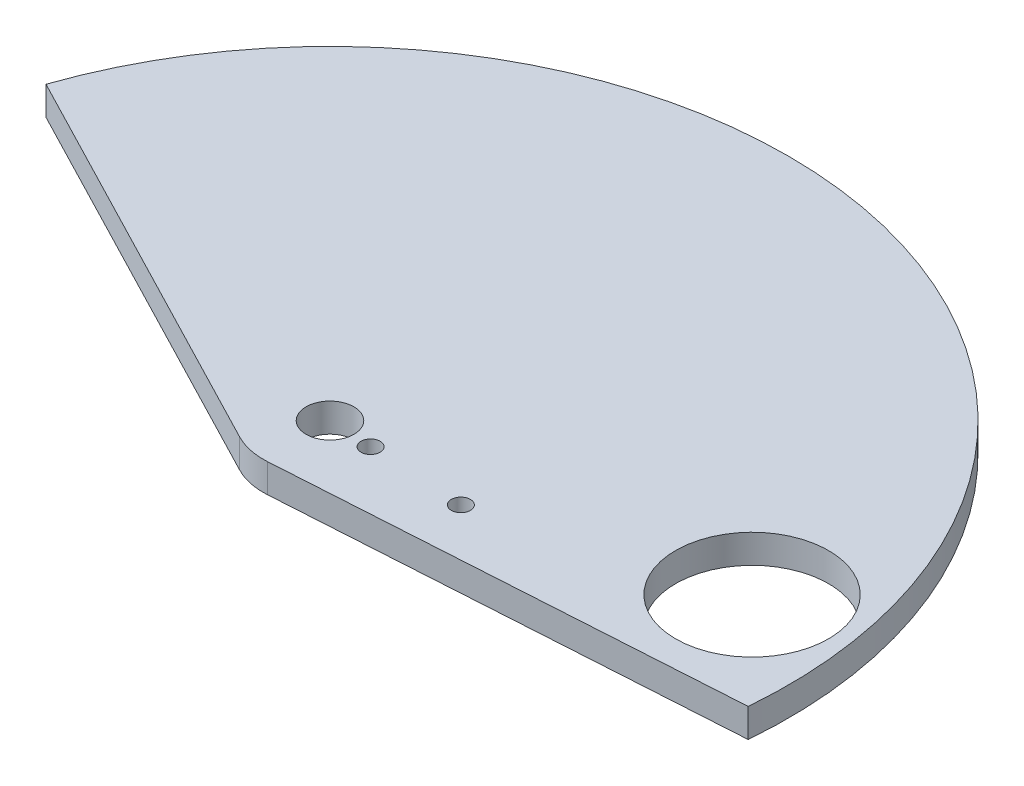
SolidWorks part; units mm, degrees
ref_plane "Front Plane" through (0, 0, 0) normal (0, 0, 1) x (1, 0, 0)
ref_plane "Top Plane" through (0, 0, 0) normal (0, 1, 0) x (1, 0, 0)
ref_plane "Right Plane" through (0, 0, 0) normal (1, 0, 0) x (0, 0, -1)
sketch "Sketch1" plane through (0, 0, 0) normal (0, 1, 0) x (1, 0, 0)
  line L0 (-38.3066, 21.6103) -> (3.7774, -0.2141)
  line L1 (7.438, -0.9863) -> (54.7516, 1.9802)
  line L2 (54.7516, 1.9802) -> (89.0001, 0.1027) construction
  line L3 (7, 6) -> (-17.3744, 35.6149) construction
  line L4 (7, 6) -> (44.8345, 12.3014) construction
  arc A0 (54.7516, 1.9802) -> (-38.3066, 21.6103) centre (7, 6) ccw
  circle A1 centre (44.8345, 12.3014) radius 8
  circle A2 centre (7, 6) radius 2.5
  circle A3 centre (21.4783, 5.2063) radius 1
  arc A4 (3.7774, -0.2141) -> (7.438, -0.9863) centre (7, 6) ccw
  arc A5 (45.0756, 1.3735) -> (-29.7001, 17.147) centre (7, 6) ccw construction
  circle A6 centre (11.4933, 5.7537) radius 1
  dimension "D1" = 2
  dimension "D4" = 120
  dimension "D3" = 16
  dimension "D7" = 5
  dimension "D2" = 7
extrude "Boss-Extrude1" add sketch "Sketch1" along normal blind 3
